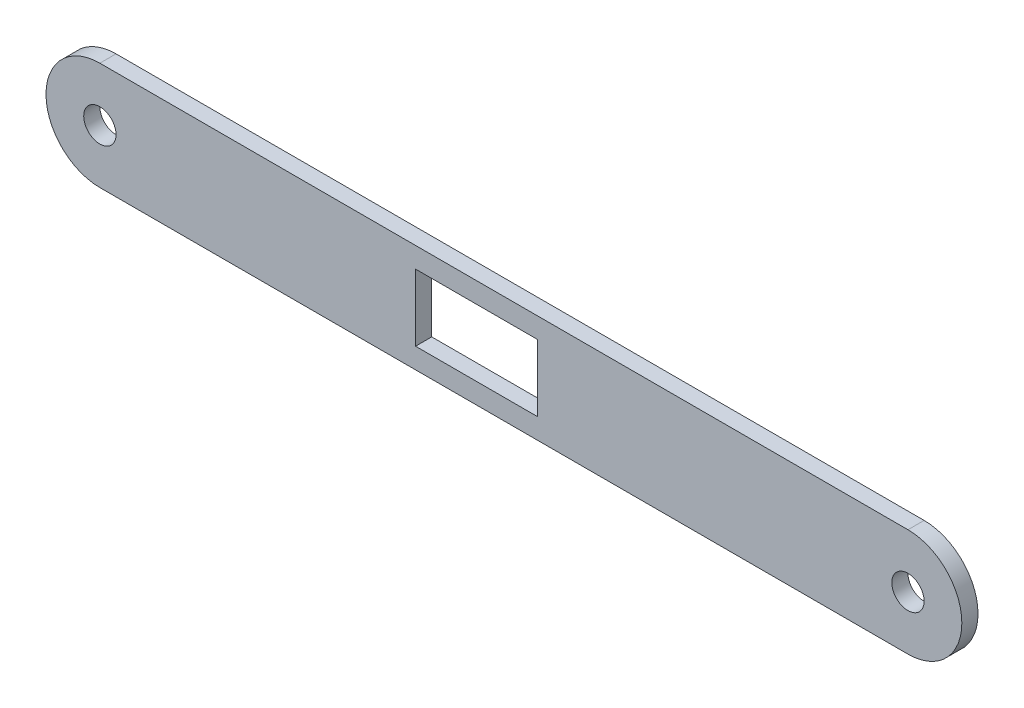
SolidWorks part; units mm, degrees
material "Acrylic (Medium-high impact)"
ref_plane "Front Plane" through (0, 0, 0) normal (0, 0, 1) x (1, 0, 0)
ref_plane "Top Plane" through (0, 0, 0) normal (0, 1, 0) x (1, 0, 0)
ref_plane "Right Plane" through (0, 0, 0) normal (1, 0, 0) x (0, 0, -1)
sketch "Sketch1" plane through (0, 0, 0) normal (0, 0, 1) x (1, 0, 0)
  line L0 (75, 0) -> (-75, 0) construction
  line L1 (75, -10) -> (-75, -10)
  line L2 (75, 10) -> (-75, 10)
  line L3 (0, 10) -> (0, -10) construction
  line L5 (-16.4, 6.2) -> (6.2, 6.2)
  line L6 (-16.4, 6.2) -> (-16.4, -6.2)
  line L7 (-16.4, -6.2) -> (6.2, -6.2)
  line L8 (6.2, 6.2) -> (6.2, -6.2)
  line L9 (-16.4, 6.2) -> (6.2, -6.2) construction
  line L10 (-16.4, -6.2) -> (6.2, 6.2) construction
  arc A0 (75, -10) -> (75, 10) centre (75, 0) ccw
  arc A1 (-75, 10) -> (-75, -10) centre (-75, 0) ccw
  circle A2 centre (75, 0) radius 3
  circle A3 centre (-75, 0) radius 3
  point P2 (0, 0)
  point P14 (-5.1, 0)
  point P21 (0, 0)
  dimension "D2" = 6
  dimension "D1" = 150
  dimension "D3" = 20
  dimension "D4" = 22.6
  dimension "D5" = 12.4
  dimension "D6" = 6.2
extrude "Boss-Extrude1" add sketch "Sketch1" along normal blind 3
